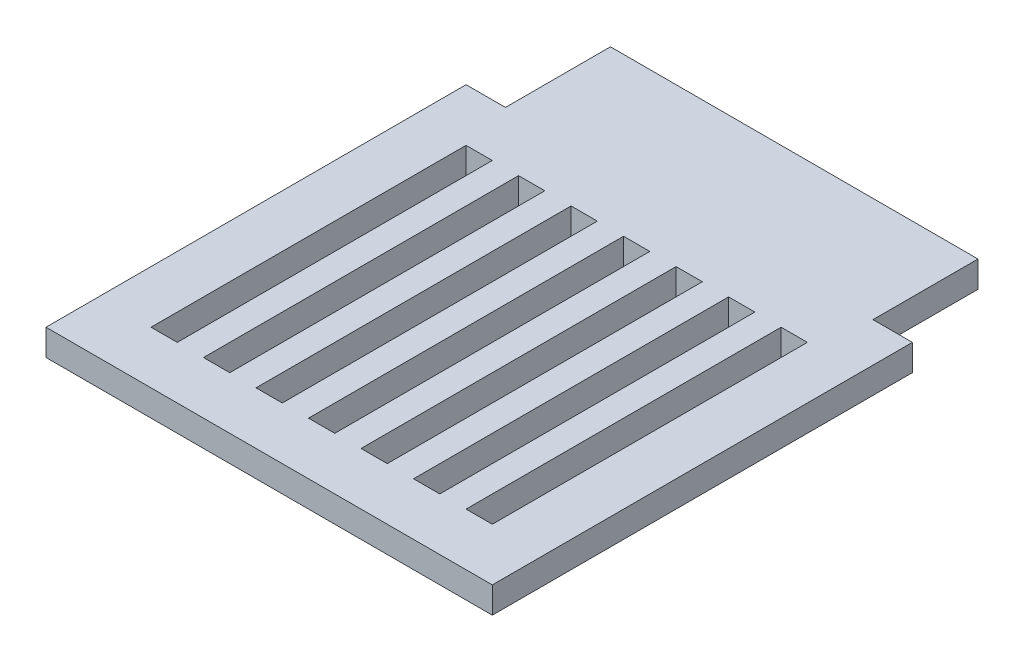
SolidWorks part; units mm, degrees
ref_plane "Front" through (0, 0, 0) normal (0, 0, 1) x (1, 0, 0)
ref_plane "Top" through (0, 0, 0) normal (0, 1, 0) x (1, 0, 0)
ref_plane "Right" through (0, 0, 0) normal (1, 0, 0) x (0, 0, -1)
sketch "草图1" plane through (0, 0, 0) normal (0, 1, 0) x (1, 0, 0)
  line L0 (-8.5, -8) -> (-8.5, 8)
  line L5 (-8.5, 8) -> (-7, 8)
  line L6 (-7, 8) -> (-7, 12)
  line L7 (-7, 12) -> (7, 12)
  line L8 (7, 12) -> (7, 8)
  line L9 (7, 8) -> (8.5, 8)
  line L10 (8.5, 8) -> (8.5, -8)
  line L11 (8.5, -8) -> (-8.5, -8)
  line L12 (0, 0) -> (0, 33.8555) construction
  line L13 (8.5, 0) -> (-16.5609, 0) construction
  point P10 (0, -8)
  dimension "D1" = 14
  dimension "D2" = 1.5
  dimension "D3" = 17
  dimension "D4" = 20
  dimension "D5" = 16
extrude "凸台-拉伸1" add sketch "草图1" along normal blind 1
sketch "草图2" plane through (0, 0, 0) normal (0, 1, 0) x (1, 0, 0)
  line L0 (7, 8) -> (7, 12) construction
  line L1 (-7, 12) -> (7, 12)
  line L2 (-7, 12) -> (-7, 13)
  line L3 (-7, 13) -> (7, 13)
  line L4 (7, 12) -> (7, 13)
  dimension "D1" = 1
extrude "凸台-拉伸2" [suppressed] add sketch "草图2" along normal blind 5.5
sketch "草图3" [suppressed] plane through (0, 5.5, 0) normal (0, 1, 0) x (1, 0, 0)
  line L0 (6.6, 13) -> (-6.61, 13) construction
  line L1 (1.995, 13) -> (-2.005, 13)
  line L2 (1.995, 13) -> (1.995, 12)
  line L3 (1.995, 12) -> (-2.005, 12)
  line L4 (-2.005, 13) -> (-2.005, 12)
  line L5 (1.995, 13) -> (-2.005, 12) construction
  line L6 (1.995, 12) -> (-2.005, 13) construction
  line L7 (6.6, 12) -> (-6.61, 12) construction
  line L8 (-0.005, 13) -> (-0.005, 14.2828) construction
  point P0 (-0.005, 12.5)
  dimension "D1" = 4
extrude "切除-拉伸1" [suppressed] cut sketch "草图3" against normal blind 3
chamfer "倒角1" [suppressed] distance 1 angle 45
sketch "草图5" plane through (0, 1, 0) normal (0, 1, 0) x (1, 0, 0)
  line L0 (0, 19.1533) -> (0, -11.8993) construction
  line L1 (-8.5, -8) -> (8.5, -8) construction
  line L2 (0.5, -6) -> (-0.5, -6)
  line L3 (0.5, -6) -> (0.5, 6)
  line L4 (0.5, 6) -> (-0.5, 6)
  line L5 (-0.5, -6) -> (-0.5, 6)
  line L6 (0.5, -6) -> (-0.5, 6) construction
  line L7 (0.5, 6) -> (-0.5, -6) construction
  line L8 (2.5, -6) -> (1.5, -6)
  line L9 (6.5, -6) -> (5.5, -6)
  line L10 (2.5, -6) -> (2.5, 6)
  line L11 (2.5, 6) -> (1.5, 6)
  line L12 (1.5, -6) -> (1.5, 6)
  line L13 (2.5, -6) -> (1.5, 6) construction
  line L14 (2.5, 6) -> (1.5, -6) construction
  line L15 (4.5, -6) -> (3.5, -6)
  line L16 (4.5, -6) -> (4.5, 6)
  line L17 (4.5, 6) -> (3.5, 6)
  line L18 (3.5, -6) -> (3.5, 6)
  line L19 (4.5, -6) -> (3.5, 6) construction
  line L20 (4.5, 6) -> (3.5, -6) construction
  line L21 (-1.5, -6) -> (-2.5, -6)
  line L22 (-1.5, -6) -> (-1.5, 6)
  line L23 (-1.5, 6) -> (-2.5, 6)
  line L24 (-2.5, -6) -> (-2.5, 6)
  line L25 (-1.5, -6) -> (-2.5, 6) construction
  line L26 (-1.5, 6) -> (-2.5, -6) construction
  line L27 (-3.5, -6) -> (-4.5, -6)
  line L28 (-3.5, -6) -> (-3.5, 6)
  line L29 (-3.5, 6) -> (-4.5, 6)
  line L30 (-4.5, -6) -> (-4.5, 6)
  line L31 (-3.5, -6) -> (-4.5, 6) construction
  line L32 (-3.5, 6) -> (-4.5, -6) construction
  line L33 (-7, 8) -> (-8.5, 8) construction
  line L34 (6.5, -6) -> (6.5, 6)
  line L35 (6.5, 6) -> (5.5, 6)
  line L36 (5.5, -6) -> (5.5, 6)
  line L37 (6.5, -6) -> (5.5, 6) construction
  line L38 (6.5, 6) -> (5.5, -6) construction
  line L39 (-5.5, -6) -> (-6.5, -6)
  line L40 (-5.5, -6) -> (-5.5, 6)
  line L41 (-5.5, 6) -> (-6.5, 6)
  line L42 (-6.5, -6) -> (-6.5, 6)
  line L43 (-5.5, -6) -> (-6.5, 6) construction
  line L44 (-5.5, 6) -> (-6.5, -6) construction
  point P3 (0, 0)
  point P10 (6, 0)
  point P13 (2, 0)
  point P18 (4, 0)
  point P23 (-2, 0)
  point P28 (-4, 0)
  point P38 (-6, 0)
  dimension "D1" = 2
  dimension "D3" = 1
  dimension "D6" = 2
  dimension "D4" = 4
  dimension "D5" = 4
extrude "切除-拉伸2" cut sketch "草图5" against normal through all
